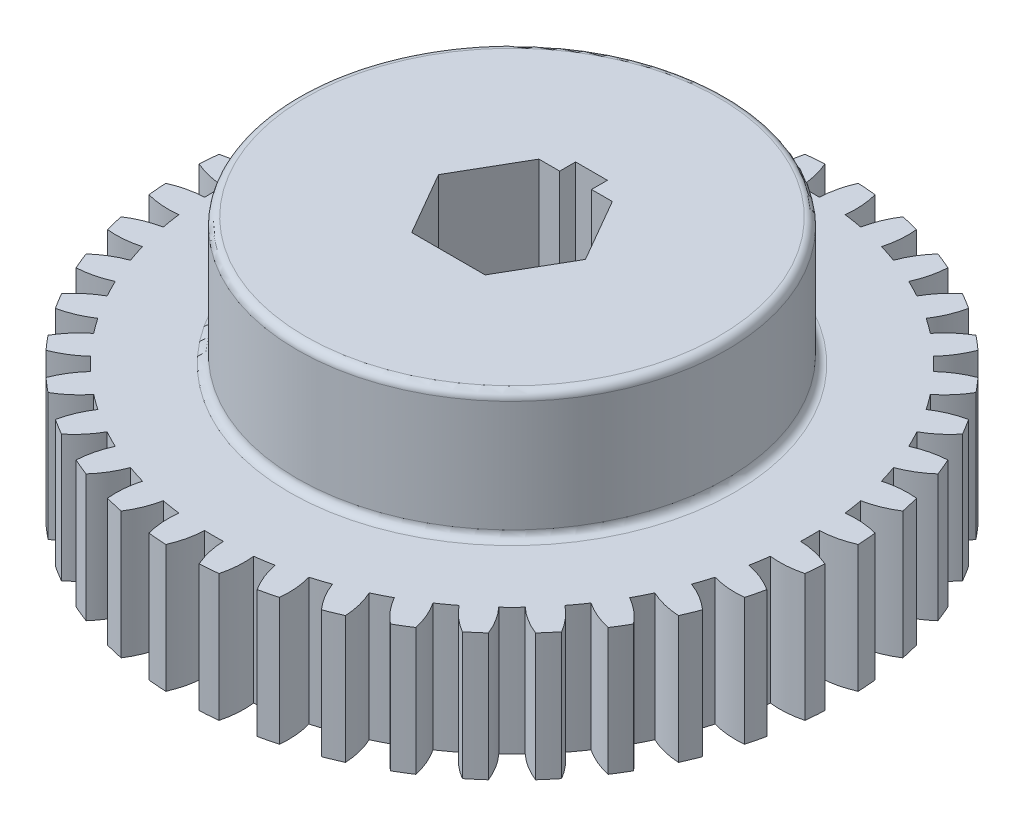
SolidWorks part; units mm, degrees
material "Alloy Steel"
ref_plane "Front Plane" through (0, 0, 0) normal (0, 0, 1) x (1, 0, 0)
ref_plane "Top Plane" through (0, 0, 0) normal (0, 1, 0) x (1, 0, 0)
ref_plane "Right Plane" through (0, 0, 0) normal (1, 0, 0) x (0, 0, -1)
sketch "Sketch1" plane through (0, 0, 0) normal (0, 1, 0) x (1, 0, 0)
  line L1 (7.3323, 0) -> (3.6662, 6.35)
  line L2 (3.6662, 6.35) -> (-3.6662, 6.35)
  line L3 (-3.6662, 6.35) -> (-7.3323, 0)
  line L4 (-7.3323, 0) -> (-3.6662, -6.35)
  line L5 (-3.6662, -6.35) -> (3.6662, -6.35)
  line L6 (3.6662, -6.35) -> (7.3323, 0)
  circle A0 centre (0, 0) radius 29.7656
  circle A1 centre (0, 0) radius 6.35 construction
  dimension "D1" = 59.5312
  dimension "D2" = 12.7
extrude "Boss-Extrude1" add sketch "Sketch1" along normal blind 12.7
sketch "Sketch2" plane through (0, 12.7, 0) normal (0, 1, 0) x (1, 0, 0)
  line L0 (3.6662, 6.35) -> (-3.6662, 6.35) construction
  line L1 (7.3323, 0) -> (3.6662, 6.35)
  line L2 (3.6662, 6.35) -> (-3.6662, 6.35)
  line L3 (-3.6662, 6.35) -> (-7.3323, 0)
  line L4 (-7.3323, 0) -> (-3.6662, -6.35)
  line L5 (-3.6662, -6.35) -> (3.6662, -6.35)
  line L6 (3.6662, -6.35) -> (7.3323, 0)
  circle A0 centre (0, 0) radius 21.4312
  circle A1 centre (0, 0) radius 6.35 construction
  dimension "D1" = 42.8625
extrude "Boss-Extrude2" add sketch "Sketch2" along normal blind 12.7
sketch "Sketch5" plane through (0, 0, 0) normal (0, 1, 0) x (1, 0, 0)
  line L0 (0, 0) -> (0, 29.7656) construction
  line L1 (0, -13.97) -> (0, 13.97) construction
  line L2 (0, 0) -> (4.6564, 29.3992) construction
  line L3 (0, 0) -> (2.5845, 32.8391) construction
  line L4 (0, 0) -> (0.935, 29.7509) construction
  line L5 (0, 0) -> (1.6666, 32.8984) construction
  arc A0 (0, 29.7656) -> (4.6564, 29.3992) centre (0, 0) cw construction
  circle A1 centre (0, 0) radius 29.7656 construction
  arc A2 (3.5004, 32.7541) -> (1.6666, 32.8984) centre (0, 0) ccw
  arc A3 (0.935, 29.7509) -> (1.6666, 32.8984) centre (9.564, 29.404) cw
  arc A4 (3.7306, 29.5309) -> (0.935, 29.7509) centre (0, 0) ccw
  arc A5 (3.7306, 29.5309) -> (3.5004, 32.7541) centre (-4.8464, 30.5381) ccw
  point P5 (2.3354, 29.6739)
  point P17 (3.5426, 33.1487)
  point P18 (2.6156, 33.2347)
  dimension "D1" = 4.6756
  dimension "D2" = 3.175
  dimension "D4" = 1.6
  dimension "D5" = 8.636
  dimension "D3" = 1.8
extrude "Boss-Extrude3" add sketch "Sketch5" along normal blind 12.7 contours A4 A5 A2 A3
pattern_circular "CirPattern1" count 40 over 360 about axis through (0, 0, 0) along (0, 1, 0) of "Boss-Extrude3"
fillet "Fillet1" radius 0.7937 2 edges at (0, 25.4, 21.4312) (0, 12.7, 21.4312)
sketch "Sketch6" plane through (0, 25.4, 0) normal (0, 1, 0) x (1, 0, 0)
  line L1 (-1.5875, 7.9375) -> (1.5875, 7.9375)
  line L2 (-1.5875, 7.9375) -> (-1.5875, 0)
  line L3 (-1.5875, 0) -> (1.5875, 0)
  line L4 (1.5875, 7.9375) -> (1.5875, 0)
  point P4 (0, 0)
  dimension "D1" = 3.175
  dimension "D2" = 7.9375
extrude "Cut-Extrude1" cut sketch "Sketch6" against normal blind 25.4
